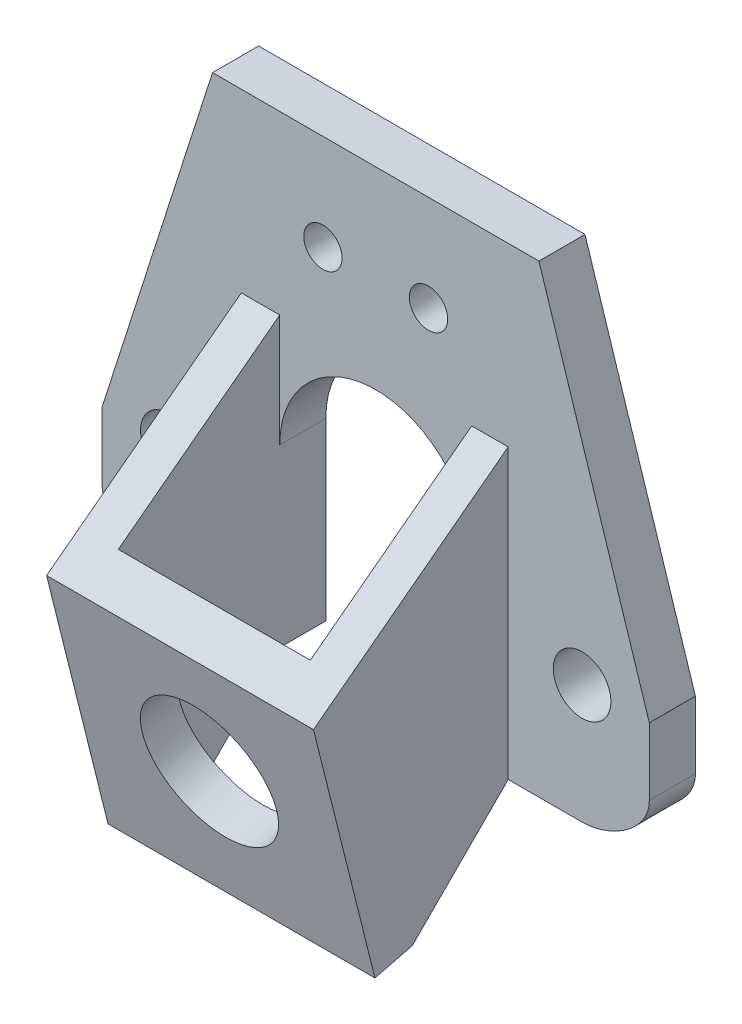
SolidWorks part; units mm, degrees
ref_plane "前视基准面" through (0, 0, 0) normal (0, 0, 1) x (1, 0, 0)
ref_plane "上视基准面" through (0, 0, 0) normal (0, 1, 0) x (1, 0, 0)
ref_plane "右视基准面" through (0, 0, 0) normal (1, 0, 0) x (0, 0, -1)
sketch "草图1" plane through (0, 0, 0) normal (0, 0, 1) x (1, 0, 0)
  line L0 (14.4365, 15.9481) -> (20.1865, 15.9481)
  line L1 (30.1865, 15.9481) -> (35.9365, 15.9481)
  line L2 (30.1865, 25.082) -> (30.1865, 15.9481)
  line L3 (20.1865, 25.082) -> (20.1865, 15.9481)
  line L4 (39.4365, 22.179) -> (39.4365, 18.679)
  line L5 (22.4365, 35.1327) -> (27.9365, 35.1327) construction
  line L6 (25.1865, 35.1327) -> (25.1865, 40.1327) construction
  line L7 (10.9365, 22.179) -> (10.9365, 18.679)
  line L8 (25.1865, 40.1327) -> (16.6865, 40.1327) construction
  line L9 (25.1865, 40.1327) -> (16.6865, 40.1327)
  line L10 (16.6865, 40.1327) -> (10.9365, 22.179)
  line L11 (33.6865, 40.1327) -> (39.4365, 22.179)
  line L12 (25.1865, 40.1327) -> (33.6865, 40.1327)
  circle A0 centre (14.4365, 22.1327) radius 1.5
  circle A1 centre (35.9365, 22.1327) radius 1.5
  arc A3 (30.1865, 25.082) -> (20.1865, 25.082) centre (25.1865, 25.082) ccw
  circle A5 centre (27.9365, 35.1327) radius 1
  circle A6 centre (22.4365, 35.1327) radius 1
  spline S0 degree 3 poles (39.4365, 18.679) (39.4365, 17.1993) (37.4163, 15.9481) (35.9365, 15.9481) knots 0 0 0 0 4.439373 4.439373 4.439373 4.439373
  spline S2 degree 3 poles (10.9365, 18.679) (10.9365, 17.1993) (12.9567, 15.9481) (14.4365, 15.9481) knots 0 0 0 0 4.439373 4.439373 4.439373 4.439373
extrude "凸台-拉伸2" add sketch "草图1" along normal blind 2.4
sketch "草图2" plane through (0, 0, 2.4) normal (0, 0, 1) x (1, 0, 0)
  line L14 (30.1865, 30.9481) -> (32.0865, 30.9481)
  line L15 (30.1865, 30.9481) -> (30.1865, 10.9481)
  line L16 (30.1865, 10.9481) -> (32.0865, 10.9481)
  line L17 (32.0865, 30.9481) -> (32.0865, 10.9481)
  line L18 (20.1865, 30.9481) -> (18.1865, 30.9481)
  line L19 (20.1865, 30.9481) -> (20.1865, 10.9481)
  line L20 (20.1865, 10.9481) -> (18.1865, 10.9481)
  line L21 (18.1865, 30.9481) -> (18.1865, 10.9481)
extrude "凸台-拉伸3" add sketch "草图2" along normal blind 10
sketch "草图4" plane through (18.1865, 0, 0) normal (-1, 0, 0) x (0, 0, 1)
  line L0 (2.4, 15.9481) -> (7.4, 10.9481)
  line L1 (12.4, 10.9481) -> (2.4, 10.9481) construction
  line L2 (2.4, 10.9481) -> (2.4, 15.9481)
  line L3 (7.4, 10.9481) -> (2.4, 10.9481)
extrude "切除-拉伸1" cut sketch "草图4" against normal blind 15
sketch "草图5" plane through (18.1865, 0, 0) normal (-1, 0, 0) x (0, 0, 1)
  line L3 (12.4, 10.9481) -> (12.4, 30.9481)
  line L4 (12.4, 30.9481) -> (7.4, 10.9481)
  line L5 (7.4, 10.9481) -> (12.4, 10.9481)
extrude "切除-拉伸2" cut sketch "草图5" against normal blind 20
sketch "草图8" plane through (0, -1.0972, 4.3887) normal (0, -0.2425, 0.9701) x (1, 0, 0)
  line L1 (18.1865, 33.0315) -> (32.0865, 33.0315)
  line L2 (18.1865, 33.0315) -> (18.1865, 12.416)
  line L3 (18.1865, 12.416) -> (32.0865, 12.416)
  line L4 (32.0865, 33.0315) -> (32.0865, 12.416)
extrude "凸台-拉伸5" add sketch "草图8" along normal blind 2
sketch "草图9" plane through (0, -1.5822, 6.329) normal (0, -0.2425, 0.9701) x (1, 0, 0)
  line L0 (18.1865, 12.416) -> (25.1365, 12.416) construction
  line L1 (18.1865, 12.416) -> (32.0865, 12.416) construction
  line L2 (25.1365, 12.416) -> (25.1365, 19.304) construction
  circle A0 centre (25.1365, 19.304) radius 3.5
extrude "切除-拉伸4" cut sketch "草图9" against normal blind 2
sketch "草图10" plane through (18.1865, 0, 0) normal (-1, 0, 0) x (0, 0, 1)
  line L0 (2.4, 30.9481) -> (12.5416, 23.2683)
  line L1 (14.3403, 30.463) -> (9.3403, 10.463) construction
  line L2 (12.5416, 23.2683) -> (18.2739, 30.9481)
  line L3 (18.2739, 30.9481) -> (2.4, 30.9481)
extrude "切除-拉伸5" cut sketch "草图10" against normal blind 20
